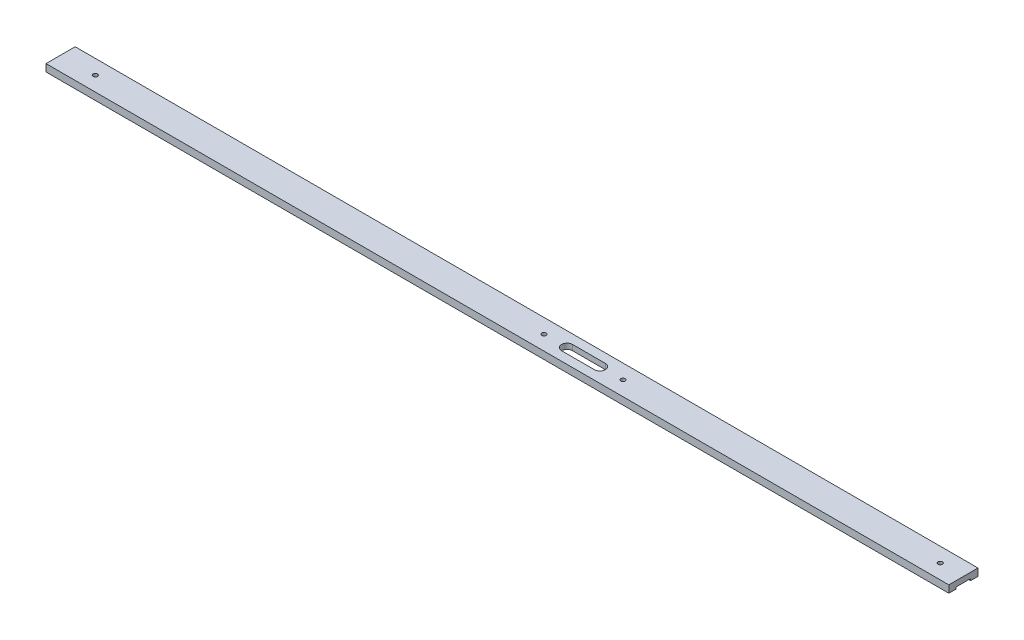
SolidWorks part; units mm, degrees
ref_plane "Front Plane" through (0, 0, 0) normal (0, 0, 1) x (1, 0, 0)
ref_plane "Top Plane" through (0, 0, 0) normal (0, 1, 0) x (1, 0, 0)
ref_plane "Right Plane" through (0, 0, 0) normal (1, 0, 0) x (0, 0, -1)
sketch "Sketch1" plane through (0, 0, 0) normal (0, 1, 0) x (1, 0, 0)
  line L1 (-123.825, -4) -> (123.825, -4)
  line L2 (-123.825, -4) -> (-123.825, 4)
  line L3 (-123.825, 4) -> (123.825, 4)
  line L4 (123.825, -4) -> (123.825, 4)
  line L5 (-123.825, -4) -> (123.825, 4) construction
  line L6 (-123.825, 4) -> (123.825, -4) construction
  point P0 (0, 0)
  dimension "D1" = 8
  dimension "D2" = 247.65
extrude "Boss-Extrude1" add sketch "Sketch1" along normal blind 2
sketch "Sketch2" plane through (123.825, 0, 0) normal (1, 0, 0) x (0, 0, -1)
  line L1 (-2, -0.5) -> (2, -0.5)
  line L2 (-2, -0.5) -> (-2, 0.5)
  line L3 (-2, 0.5) -> (2, 0.5)
  line L4 (2, -0.5) -> (2, 0.5)
  line L5 (-2, -0.5) -> (2, 0.5) construction
  line L6 (-2, 0.5) -> (2, -0.5) construction
  line L7 (-4, 0) -> (4, 0) construction
  point P6 (0, 0)
  point P7 (0, 0.5)
  point P8 (-2, 0)
  dimension "D1" = 4
  dimension "D2" = 1
extrude "Cut-Extrude1" cut sketch "Sketch2" against normal through all
sketch "Sketch5" plane through (0, 0.5, 0) normal (0, 1, 0) x (-1, 0, 0)
  line L0 (-15.1088, 0) -> (-24.1088, 0) construction
  line L1 (-15.1088, -1.5) -> (-24.1088, -1.5)
  line L2 (-15.1088, 1.5) -> (-24.1088, 1.5)
  arc A0 (-15.1088, -1.5) -> (-15.1088, 1.5) centre (-15.1088, 0) ccw
  arc A1 (-24.1088, 1.5) -> (-24.1088, -1.5) centre (-24.1088, 0) ccw
  point P2 (-19.6088, 0)
extrude "Cut-Extrude2" cut sketch "Sketch5" along normal through all
hole_wizard "#23 (0.154) Diameter Hole1" positions "Sketch9" profile "Sketch8" hole size "#23" standard "Ansi Inch"
sketch "Sketch9" plane through (0, 2, 0) normal (0, 1, 0) x (-1, 0, 0)
  line L0 (123.825, -4) -> (123.825, 4) construction
  point P1 (118.825, 0)
  point P4 (108.825, 0)
  point P14 (123.825, 0)
  dimension "D1" = 5
  dimension "D2" = 15
sketch "Sketch8" plane through (-118.825, 2, 0) normal (1, 0, 0) x (0, 0, 1)
  line L0 (0, 0) -> (0, 3.2072)
  line L1 (0, 3.2072) -> (1.9558, 2.032)
  line L2 (1.9558, 2.032) -> (1.9558, 0)
  line L5 (1.9558, 0) -> (0, 0)
  line L10 (0, 3.2072) -> (-1.9558, 2.032) construction
  line L11 (0, -6.35) -> (0, 107.95) construction
  dimension "Hole Dia." = 3.9116
  dimension "Hole Depth" = 2.032
  dimension "Drill Angle" = 118
hole_wizard "#0-80 Tapped Hole1" positions "Sketch11" profile "Sketch10" tap size "#0-80" standard "Ansi Inch"
sketch "Sketch11" plane through (0, 2, 0) normal (0, 1, 0) x (-1, 0, 0)
  line L0 (-123.825, 4) -> (-123.825, -4) construction
  line L1 (123.825, -4) -> (123.825, 4) construction
  arc A0 (-24.1088, 1.5) -> (-24.1088, -1.5) centre (-24.1088, 0) ccw construction
  arc A1 (-15.1088, -1.5) -> (-15.1088, 1.5) centre (-15.1088, 0) ccw construction
  point P3 (114.3, 0)
  point P5 (-8.7588, 0)
  point P7 (-30.4588, 0)
  point P9 (-117.475, 0)
  point P15 (-123.825, 0)
  dimension "D1" = 9.525
  dimension "D2" = 6.35
  dimension "D3" = 6.35
  dimension "D4" = 6.35
sketch "Sketch10" plane through (-114.3, 2, 0) normal (1, 0, 0) x (0, 0, 1)
  line L0 (0, 0) -> (0, 4.9299)
  line L1 (0, 4.9299) -> (0.5956, 4.572)
  line L2 (0.5956, 4.572) -> (0.5956, 0)
  line L5 (0.5956, 0) -> (0, 0)
  line L10 (0, 4.9299) -> (-0.5956, 4.572) construction
  line L11 (0, -6.35) -> (0, 107.95) construction
  dimension "Tap Drill Dia." = 1.1913
  dimension "Tap Drill Depth" = 4.572
  dimension "Drill Angle" = 118
